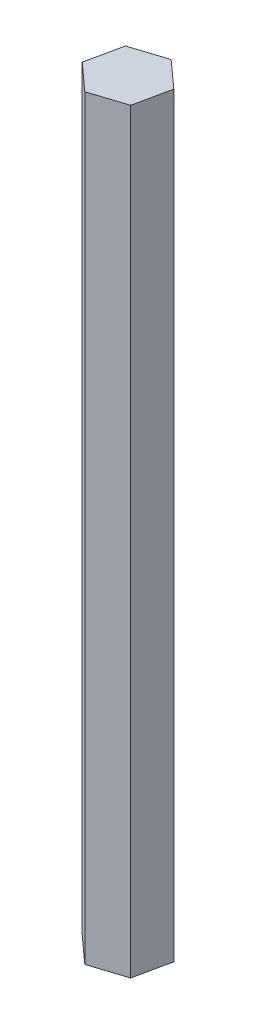
SolidWorks part; units mm, degrees
ref_plane "Front Plane" through (0, 0, 0) normal (0, 0, 1) x (1, 0, 0)
ref_plane "Top Plane" through (0, 0, 0) normal (0, 1, 0) x (1, 0, 0)
ref_plane "Right Plane" through (0, 0, 0) normal (1, 0, 0) x (0, 0, -1)
sketch "Sketch1" plane through (0, 0, 0) normal (0, 1, 0) x (1, 0, 0)
  line L7 (2.0836, -0.3657) -> (3.6227, 6.8033)
  line L8 (3.6227, 6.8033) -> (-1.8163, 11.7207)
  line L9 (-1.8163, 11.7207) -> (-8.7944, 9.4691)
  line L10 (-8.7944, 9.4691) -> (-10.3335, 2.3001)
  line L11 (-10.3335, 2.3001) -> (-4.8945, -2.6173)
  line L12 (-4.8945, -2.6173) -> (2.0836, -0.3657)
  circle A0 centre (-3.3554, 4.5517) radius 6.35 construction
  dimension "D1" = 12.7
extrude "Boss-Extrude1" add sketch "Sketch1" along normal blind 152.4
